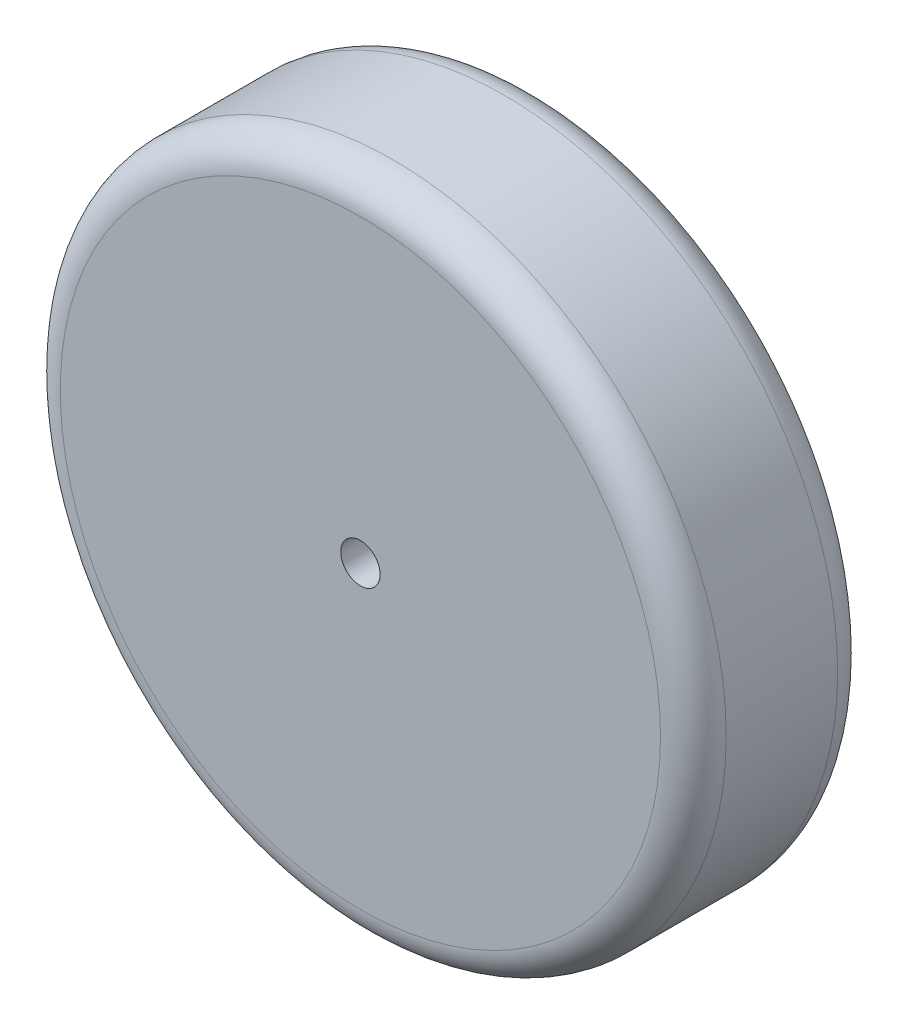
SolidWorks part; units mm, degrees
ref_plane "前基準面" through (0, 0, 0) normal (0, 0, 1) x (1, 0, 0)
ref_plane "上基準面" through (0, 0, 0) normal (0, 1, 0) x (1, 0, 0)
ref_plane "右基準面" through (0, 0, 0) normal (1, 0, 0) x (0, 0, -1)
sketch "草圖1" plane through (0, 0, 0) normal (0, 0, 1) x (1, 0, 0)
  circle A0 centre (0, 0) radius 101.5
  dimension "D1" = 203
extrude "填料-伸長1" add sketch "草圖1" along normal blind 54
fillet "圓角1" radius 10 2 edges at (101.5, 0, 0) (101.5, 0, 54)
sketch "草圖2" plane through (0, 0, 0) normal (0, 0, -1) x (-1, 0, 0)
  circle A0 centre (0, 0) radius 6
  dimension "D1" = 12
extrude "除料-伸長1" cut sketch "草圖2" against normal blind 54 contours A0
